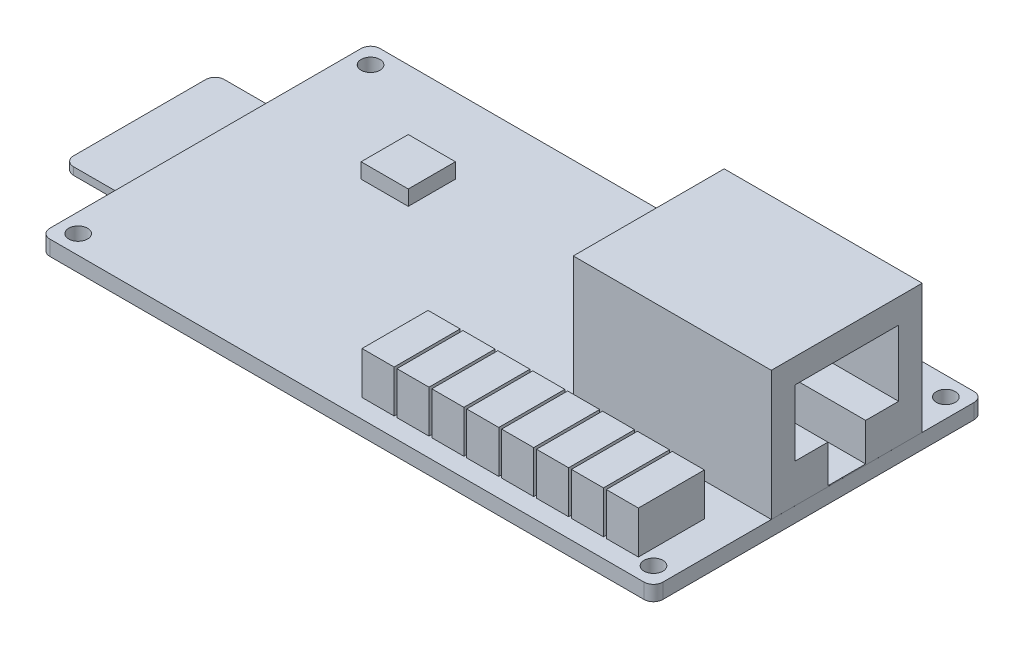
SolidWorks part; units mm, degrees
ref_plane "Ebene vorne" through (0, 0, 0) normal (0, 0, 1) x (1, 0, 0)
ref_plane "Ebene oben" through (0, 0, 0) normal (0, 1, 0) x (1, 0, 0)
ref_plane "Ebene rechts" through (0, 0, 0) normal (1, 0, 0) x (0, 0, -1)
sketch "Skizze1" plane through (0, 0, 0) normal (0, 1, 0) x (1, 0, 0)
  line L0 (-76.2443, 0) -> (88.5754, 0) construction
  line L1 (0, 66.6052) -> (0, -54.2742) construction
  line L2 (-32.5, -17.5) -> (-32.5, 17.5)
  line L3 (-32.5, 17.5) -> (32.5, 17.5)
  line L4 (32.5, -17.5) -> (32.5, 17.5)
  line L5 (-32.5, -17.5) -> (32.5, -17.5)
  circle A0 centre (-30.5, -15.5) radius 1
  circle A1 centre (30.5, -15.5) radius 1
  circle A2 centre (30.5, 15.5) radius 1
  circle A3 centre (-30.5, 15.5) radius 1
  point P9 (0, 17.5)
  point P10 (0, -17.5)
  point P12 (32.5, 0)
  point P13 (-32.5, 0)
  dimension "D3" = 2
  dimension "D4" = 61
  dimension "D1" = 65
  dimension "D2" = 35
  dimension "D5" = 31
extrude "Aufsatz-Linear austragen1" add sketch "Skizze1" along normal blind 1.6
fillet "Verrundung1" radius 1 4 edges at (-32.5, 0.8, 17.5) (32.5, 0.8, 17.5) (32.5, 0.8, -17.5) (-32.5, 0.8, -17.5)
sketch "Skizze2" plane through (0, 0, 0) normal (0, -1, 0) x (1, 0, 0)
  line L0 (41.952, 0) -> (-41.6687, 0) construction
  line L1 (-14.49, 8) -> (-14.49, -8)
  line L2 (-14.49, -8) -> (-32.49, -8)
  line L3 (-32.49, -8) -> (-32.49, 8)
  line L4 (-14.49, 8) -> (-32.49, 8)
  line L8 (-32.5, -16.5) -> (-32.5, 16.5) construction
  point P8 (-32.49, 0)
  point P9 (-14.49, 0)
  dimension "D1" = 18
  dimension "D2" = 16
  dimension "D3" = 0.01
extrude "Aufsatz-Linear austragen2" add sketch "Skizze2" along normal blind 3
sketch "Skizze3" plane through (-32.49, 0, 0) normal (-1, 0, 0) x (0, 0, 1)
  line L0 (0, -18.2559) -> (0, 7.445) construction
  line L1 (7.999, -0.001) -> (7.999, -0.801)
  line L2 (-16.5, 0) -> (16.5, 0) construction
  line L3 (7.999, -0.801) -> (-7.999, -0.801)
  line L4 (7.999, -0.001) -> (-7.999, -0.001)
  line L6 (-7.999, -0.001) -> (-7.999, -0.801)
  line L7 (8, -3) -> (8, 0) construction
  point P12 (0, 0)
  point P13 (0, -0.801)
  dimension "D1" = 0.8
  dimension "D2" = 0.001
  dimension "D3" = 0.001
extrude "Aufsatz-Linear austragen3" add sketch "Skizze3" along normal blind 7
fillet "Verrundung2" radius 1 2 edges at (-39.49, -0.401, -7.999) (-39.49, -0.401, 7.999)
sketch "Skizze4" plane through (0, 1.6, 0) normal (0, 1, 0) x (1, 0, 0)
  line L0 (42.5966, 3) -> (-19.5986, 3) construction
  line L1 (32.499, -5) -> (11.499, -5)
  line L3 (11.499, -5) -> (11.499, 11)
  line L4 (32.499, -5) -> (32.499, 11)
  line L5 (32.499, 11) -> (11.499, 11)
  line L6 (-10.065, 0) -> (10.065, 0) construction
  line L7 (31.5, 17.5) -> (-31.5, 17.5) construction
  line L8 (-31.5, -17.5) -> (31.5, -17.5) construction
  line L10 (32.5, -16.5) -> (32.5, 16.5) construction
  point P12 (32.499, 3)
  point P13 (11.499, 3)
  dimension "D1" = 21
  dimension "D2" = 16
  dimension "D3" = 3
  dimension "D4" = 6.5
  dimension "D5" = 12.5
  dimension "D6" = 0.001
extrude "Aufsatz-Linear austragen4" add sketch "Skizze4" along normal blind 13.7
sketch "Skizze5" plane through (32.499, 0, 0) normal (1, 0, 0) x (0, 0, -1)
  line L0 (3, 29.2354) -> (3, -18.6456) construction
  line L1 (8.5, 12.7) -> (-2.5, 12.7)
  line L2 (-2.5, 12.7) -> (-2.5, 5.7)
  line L3 (-2.5, 5.7) -> (1, 5.7)
  line L4 (1, 5.7) -> (1, 1.7)
  line L5 (1, 1.7) -> (5, 1.7)
  line L6 (5, 5.7) -> (5, 1.7)
  line L7 (8.5, 5.7) -> (5, 5.7)
  line L8 (8.5, 12.7) -> (8.5, 5.7)
  line L9 (0, 10.065) -> (0, -10.065) construction
  line L10 (-5, 15.3) -> (11, 15.3) construction
  point P10 (3, 1.7)
  point P13 (3, 12.7)
  dimension "D1" = 3
  dimension "D2" = 11
  dimension "D3" = 7
  dimension "D4" = 11
  dimension "D5" = 2.6
  dimension "D6" = 4
extrude "Schnitt-Linear austragen1" cut sketch "Skizze5" against normal blind 12
sketch "Skizze6" plane through (0, 1.6, 0) normal (0, 1, 0) x (1, 0, 0)
  line L0 (32.5, -16.5) -> (32.5, 16.5) construction
  line L1 (28.9, -15.5) -> (25.5, -15.5)
  line L2 (28.9, -15.5) -> (28.9, -8.5)
  line L3 (28.9, -8.5) -> (25.5, -8.5)
  line L4 (25.5, -15.5) -> (25.5, -8.5)
  line L5 (36.8302, -12) -> (-8.7832, -12) construction
  line L6 (-31.5, -17.5) -> (31.5, -17.5) construction
  line L7 (25.2, -15.5) -> (21.8, -15.5)
  line L8 (25.2, -15.5) -> (25.2, -8.5)
  line L9 (25.2, -8.5) -> (21.8, -8.5)
  line L10 (21.8, -15.5) -> (21.8, -8.5)
  line L11 (21.5, -15.5) -> (18.1, -15.5)
  line L12 (21.5, -15.5) -> (21.5, -8.5)
  line L13 (21.5, -8.5) -> (18.1, -8.5)
  line L14 (18.1, -15.5) -> (18.1, -8.5)
  line L15 (17.8, -15.5) -> (14.4, -15.5)
  line L16 (17.8, -15.5) -> (17.8, -8.5)
  line L17 (17.8, -8.5) -> (14.4, -8.5)
  line L18 (14.4, -15.5) -> (14.4, -8.5)
  line L19 (14.1, -15.5) -> (10.7, -15.5)
  line L20 (14.1, -15.5) -> (14.1, -8.5)
  line L21 (14.1, -8.5) -> (10.7, -8.5)
  line L22 (10.7, -15.5) -> (10.7, -8.5)
  line L23 (10.4, -15.5) -> (7, -15.5)
  line L24 (10.4, -15.5) -> (10.4, -8.5)
  line L25 (10.4, -8.5) -> (7, -8.5)
  line L26 (7, -15.5) -> (7, -8.5)
  line L27 (6.7, -15.5) -> (3.3, -15.5)
  line L28 (6.7, -15.5) -> (6.7, -8.5)
  line L29 (6.7, -8.5) -> (3.3, -8.5)
  line L30 (3.3, -15.5) -> (3.3, -8.5)
  line L31 (3, -15.5) -> (-0.4, -15.5)
  line L32 (3, -15.5) -> (3, -8.5)
  line L33 (3, -8.5) -> (-0.4, -8.5)
  line L34 (-0.4, -15.5) -> (-0.4, -8.5)
  dimension "D1" = 7
  dimension "D2" = 3.4
  dimension "D3" = 3.6
  dimension "D4" = 5.5
  dimension "D6" = 2
  dimension "D5" = 8
extrude "Aufsatz-Linear austragen5" add sketch "Skizze6" along normal blind 4.5
sketch "Skizze7" plane through (0, 0, 0) normal (0, -1, 0) x (1, 0, 0)
  line L0 (-52.0475, 0) -> (40.4968, 0) construction
  line L1 (0, 30.3691) -> (0, -25.1141) construction
  line L2 (-3, -2.5) -> (-3, 2.5)
  line L3 (-3, 2.5) -> (2, 2.5)
  line L4 (2, 2.5) -> (2, -2.5)
  line L5 (-3, -2.5) -> (2, -2.5)
  line L6 (-0.5, 10.3714) -> (-0.5, -7.7217) construction
  line L7 (32.5, 16.5) -> (32.5, -16.5) construction
  point P10 (2, 0)
  point P11 (-3, 0)
  dimension "D1" = 5
  dimension "D2" = 5
  dimension "D3" = 33
extrude "Aufsatz-Linear austragen6" add sketch "Skizze7" along normal blind 1.8
sketch "Skizze8" plane through (0, 1.6, 0) normal (0, 1, 0) x (1, 0, 0)
  line L0 (-20.5, 9.5) -> (-20.5, 4.5)
  line L1 (-20.5, 4.5) -> (-15.5, 4.5)
  line L2 (-15.5, 4.5) -> (-15.5, 9.5)
  line L3 (-15.5, 9.5) -> (-20.5, 9.5)
  line L4 (-31.5, -17.5) -> (31.5, -17.5) construction
  line L5 (-32.5, 16.5) -> (-32.5, -16.5) construction
  dimension "D1" = 5
  dimension "D2" = 22
  dimension "D3" = 12
extrude "Aufsatz-Linear austragen7" add sketch "Skizze8" along normal blind 1.6
